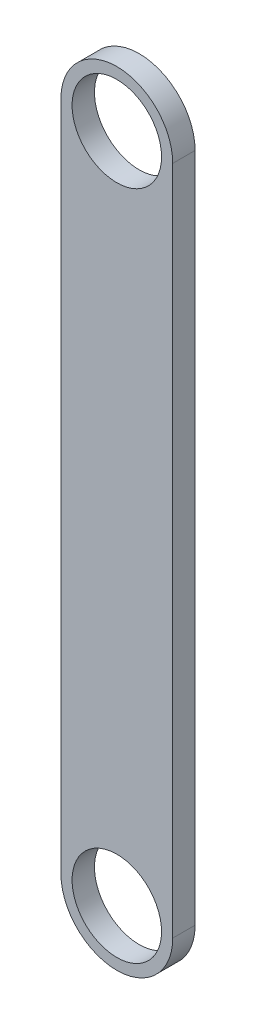
SolidWorks part; units mm, degrees
ref_plane "Front Plane" through (0, 0, 0) normal (0, 0, 1) x (1, 0, 0)
ref_plane "Top Plane" through (0, 0, 0) normal (0, 1, 0) x (1, 0, 0)
ref_plane "Right Plane" through (0, 0, 0) normal (1, 0, 0) x (0, 0, -1)
sketch "Sketch1" plane through (0, 0, 0) normal (0, 0, 1) x (1, 0, 0)
  line L0 (0, -150) -> (0, 150) construction
  line L1 (-25, -150) -> (-25, 150)
  line L2 (25, -150) -> (25, 150)
  arc A0 (-25, -150) -> (25, -150) centre (0, -150) ccw
  arc A1 (25, 150) -> (-25, 150) centre (0, 150) ccw
  circle A2 centre (0, 150) radius 20
  circle A3 centre (0, -150) radius 20
  point P2 (0, 0)
  dimension "D1" = 25
  dimension "D3" = 40
  dimension "D4" = 40
  dimension "D5" = 25
  dimension "D2" = 300
extrude "Boss-Extrude1" add sketch "Sketch1" along normal blind 10
scale "Scale2" scale about centroid uniform scaling yes scale factor 0.1
